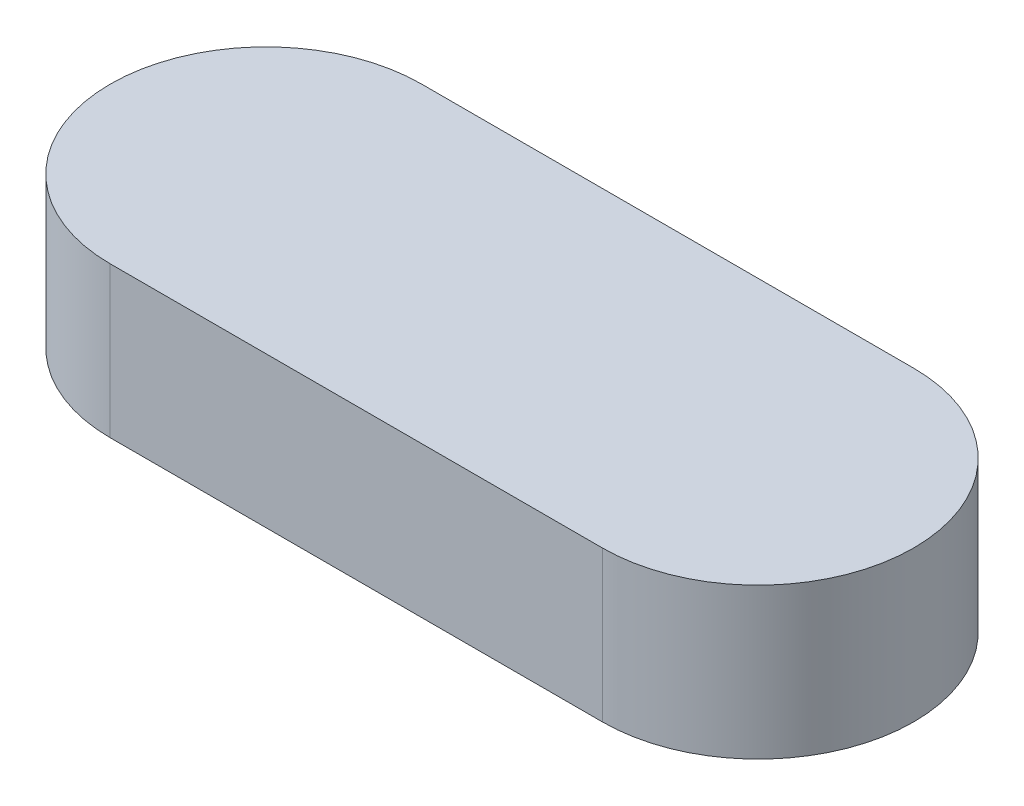
SolidWorks part; units mm, degrees
ref_plane "Front Plane" through (0, 0, 0) normal (0, 0, 1) x (1, 0, 0)
ref_plane "Top Plane" through (0, 0, 0) normal (0, 1, 0) x (1, 0, 0)
ref_plane "Right Plane" through (0, 0, 0) normal (1, 0, 0) x (0, 0, -1)
sketch "Sketch1" plane through (0, 0, 0) normal (0, 1, 0) x (1, 0, 0)
  line L0 (-12.25, 0) -> (12.25, 0) construction
  line L1 (-12.25, 7.75) -> (12.25, 7.75)
  line L2 (-12.25, -7.75) -> (12.25, -7.75)
  arc A0 (-12.25, 7.75) -> (-12.25, -7.75) centre (-12.25, 0) ccw
  arc A1 (12.25, -7.75) -> (12.25, 7.75) centre (12.25, 0) ccw
  point P2 (0, 0)
  dimension "D2" = 7.75
  dimension "D1" = 24.5
extrude "Boss-Extrude1" add sketch "Sketch1" along normal blind 7.5
